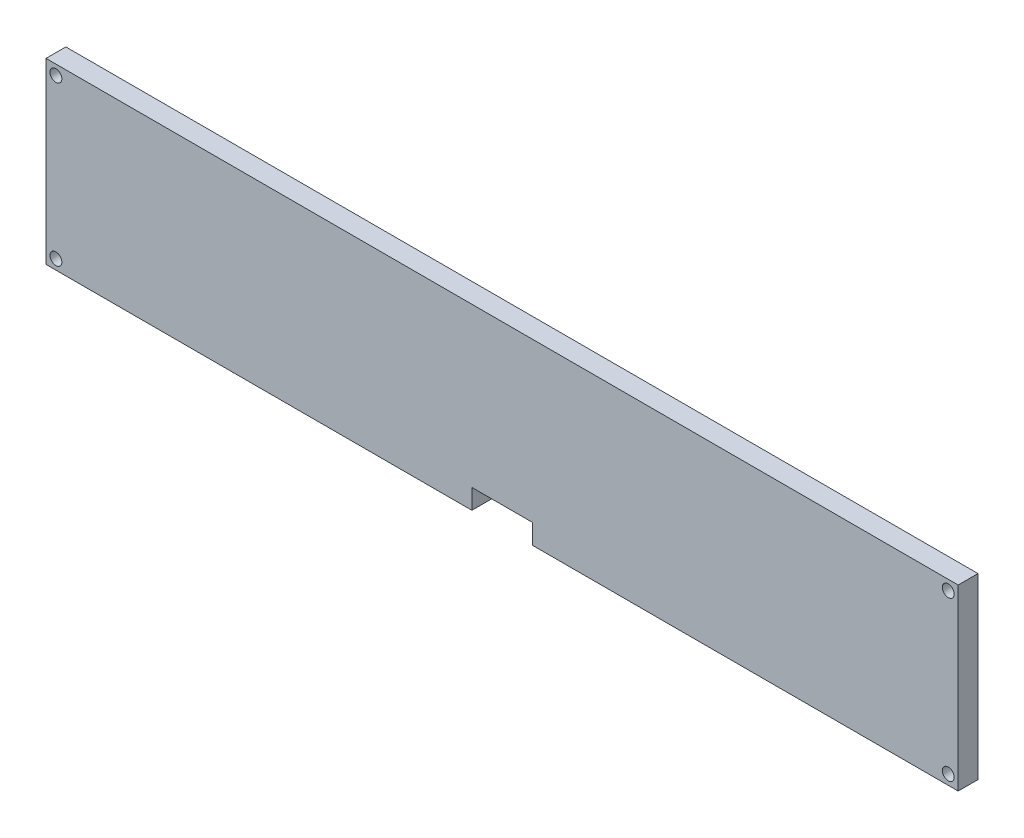
SolidWorks part; units mm, degrees
ref_plane "Front Plane" through (0, 0, 0) normal (0, 0, 1) x (1, 0, 0)
ref_plane "Top Plane" through (0, 0, 0) normal (0, 1, 0) x (1, 0, 0)
ref_plane "Right Plane" through (0, 0, 0) normal (1, 0, 0) x (0, 0, -1)
sketch "Sketch1" plane through (0, 0, 0) normal (0, 0, 1) x (1, 0, 0)
  line L1 (0, 0) -> (230, 0)
  line L2 (0, 0) -> (0, 45)
  line L3 (0, 45) -> (230, 45)
  line L4 (230, 0) -> (230, 45)
  dimension "D1" = 230
  dimension "D2" = 45
extrude "Boss-Extrude1" add sketch "Sketch1" along normal blind 5
sketch "Sketch2" plane through (0, 0, 0) normal (0, 0, -1) x (-1, 0, 0)
  line L0 (-235, 0) -> (-235, 45) construction
  line L1 (-230, 45) -> (0, 45) construction
  line L2 (-230, 22.5) -> (0, 22.5) construction
  line L3 (-230, 45) -> (-230, 0) construction
  line L4 (0, 45) -> (0, 0) construction
  line L5 (-115, 22.5) -> (-115, 45) construction
  circle A0 centre (-227.5, 42.5) radius 1.5
  circle A1 centre (-227.5, 2.5) radius 1.5
  circle A2 centre (-2.5, 2.5) radius 1.5
  circle A3 centre (-2.5, 42.5) radius 1.5
  dimension "D1" = 3
  dimension "D2" = 7.5
  dimension "D3" = 2.5
extrude "Cut-Extrude1" cut sketch "Sketch2" against normal blind 10
sketch "Sketch3" plane through (0, 0, 0) normal (0, 0, -1) x (-1, 0, 0)
  line L0 (0, 0) -> (-230, 0) construction
  line L1 (-122.62, -5) -> (-107.38, -5)
  line L2 (-122.62, -5) -> (-122.62, 5)
  line L3 (-122.62, 5) -> (-107.38, 5)
  line L4 (-107.38, -5) -> (-107.38, 5)
  line L5 (-122.62, -5) -> (-107.38, 5) construction
  line L6 (-122.62, 5) -> (-107.38, -5) construction
  point P0 (-115, 0)
  dimension "D1" = 15.24
  dimension "D2" = 10
extrude "Cut-Extrude2" cut sketch "Sketch3" against normal up to surface (5 mm away) up to face at (1, 42.5, 5)
